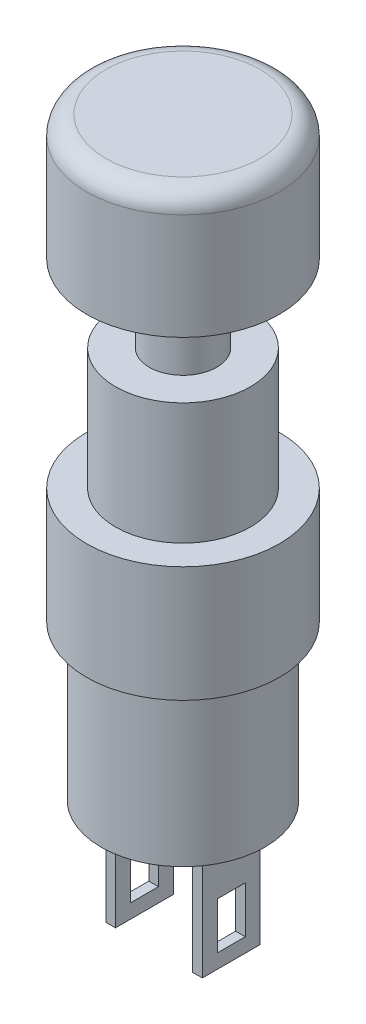
SolidWorks part; units mm, degrees
ref_plane "Plano frontal" through (0, 0, 0) normal (0, 0, 1) x (1, 0, 0)
ref_plane "Plano superior" through (0, 0, 0) normal (0, 1, 0) x (1, 0, 0)
ref_plane "Plano direito" through (0, 0, 0) normal (1, 0, 0) x (0, 0, -1)
sketch "Esboço1" plane through (0, 0, 0) normal (0, 1, 0) x (1, 0, 0)
  circle A0 centre (0, 0) radius 5
  dimension "D1" = 10
extrude "Ressalto-extrusão1" add sketch "Esboço1" along normal blind 6
sketch "Esboço2" plane through (0, 0, 0) normal (0, -1, 0) x (1, 0, 0)
  circle A0 centre (0, 0) radius 4.25
  dimension "D1" = 8.5
extrude "Ressalto-extrusão2" add sketch "Esboço2" along normal blind 8
sketch "Esboço3" plane through (0, -8, 0) normal (0, -1, 0) x (1, 0, 0)
  line L0 (0, 4.25) -> (0, -4.25) construction
  line L1 (0, 0) -> (4.25, 0) construction
  line L2 (2, -1.5) -> (2.5, -1.5)
  line L3 (2, -1.5) -> (2, 1.5)
  line L4 (2, 1.5) -> (2.5, 1.5)
  line L5 (2.5, -1.5) -> (2.5, 1.5)
  line L6 (2, -1.5) -> (2.5, 1.5) construction
  line L7 (2, 1.5) -> (2.5, -1.5) construction
  line L8 (-2, 1.5) -> (-2.5, -1.5) construction
  line L9 (-2, -1.5) -> (-2.5, 1.5) construction
  line L10 (-2.5, -1.5) -> (-2.5, 1.5)
  line L11 (-2, 1.5) -> (-2.5, 1.5)
  line L12 (-2, -1.5) -> (-2, 1.5)
  line L13 (-2, -1.5) -> (-2.5, -1.5)
  circle A0 centre (0, 0) radius 4.25 construction
  circle A1 centre (0, 0) radius 4.25 construction
  point P7 (2.25, 0)
  point P19 (-2.25, 0)
  dimension "D1" = 0.5
  dimension "D2" = 3
  dimension "D3" = 4.5
extrude "Ressalto-extrusão3" add sketch "Esboço3" along normal blind 6
sketch "Esboço4" plane through (-2.5, 0, 0) normal (-1, 0, 0) x (0, 0, 1)
  line L1 (-0.7286, -13.2622) -> (0.7144, -13.2622)
  line L2 (-0.7286, -13.2622) -> (-0.7286, -10.8387)
  line L3 (-0.7286, -10.8387) -> (0.7144, -10.8387)
  line L4 (0.7144, -13.2622) -> (0.7144, -10.8387)
extrude "Corte-extrusão1" cut sketch "Esboço4" against normal through all
sketch "Esboço5" plane through (0, 6, 0) normal (0, 1, 0) x (1, 0, 0)
  circle A0 centre (0, 0) radius 3.5
  dimension "D1" = 7
extrude "Ressalto-extrusão4" add sketch "Esboço5" along normal blind 6.3
sketch "Esboço6" plane through (0, 12.3, 0) normal (0, 1, 0) x (1, 0, 0)
  circle A0 centre (0, 0) radius 1.75
  dimension "D1" = 3.5
extrude "Ressalto-extrusão5" add sketch "Esboço6" along normal blind 4
sketch "Esboço7" plane through (0, 16.3, 0) normal (0, 1, 0) x (1, 0, 0)
  circle A0 centre (0, 0) radius 5
  dimension "D1" = 10
extrude "Ressalto-extrusão6" add sketch "Esboço7" along normal blind 6.5
fillet "Filete1" radius 1 1 edges at (0, 22.8, 5)
